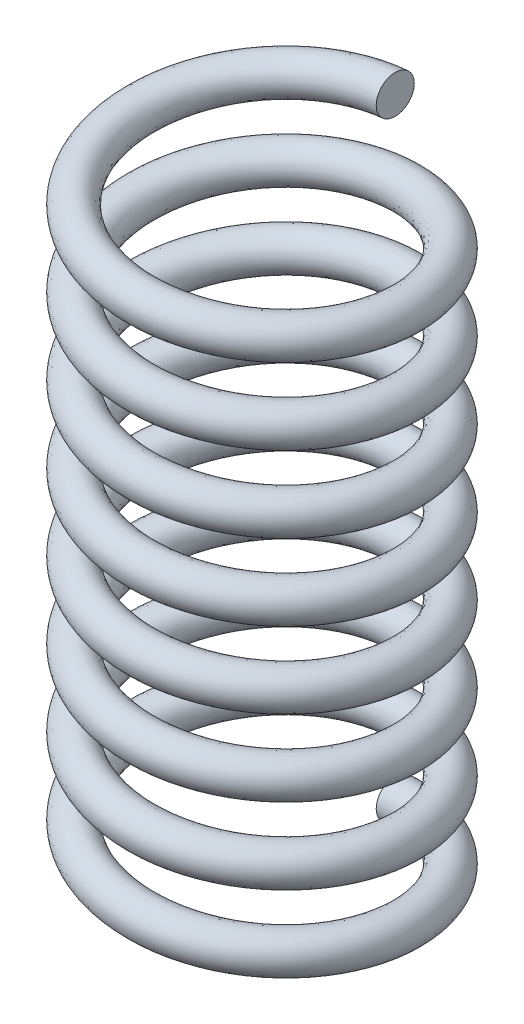
SolidWorks part; units mm, degrees
ref_plane "Front Plane" through (0, 0, 0) normal (0, 0, 1) x (1, 0, 0)
ref_plane "Top Plane" through (0, 0, 0) normal (0, 1, 0) x (1, 0, 0)
ref_plane "Right Plane" through (0, 0, 0) normal (1, 0, 0) x (0, 0, -1)
sketch "Sketch4" plane through (0, 0, 0) normal (0, 1, 0) x (1, 0, 0)
  circle A0 centre (0, 0) radius 35
  point P3 (239.4743, -198.4166)
  dimension "D1" = 70
curve "Helix/Spiral3" pitch 20 height 160 turns 8
sketch "Sketch5" plane through (0, 0, 0) normal (1, 0, 0) x (0, 0, -1)
  circle A0 centre (-34.9999, 10) radius 5
  dimension "D1" = 10
sweep "Sweep3" add profiles "Sketch5" path "Helix/Spiral3"
